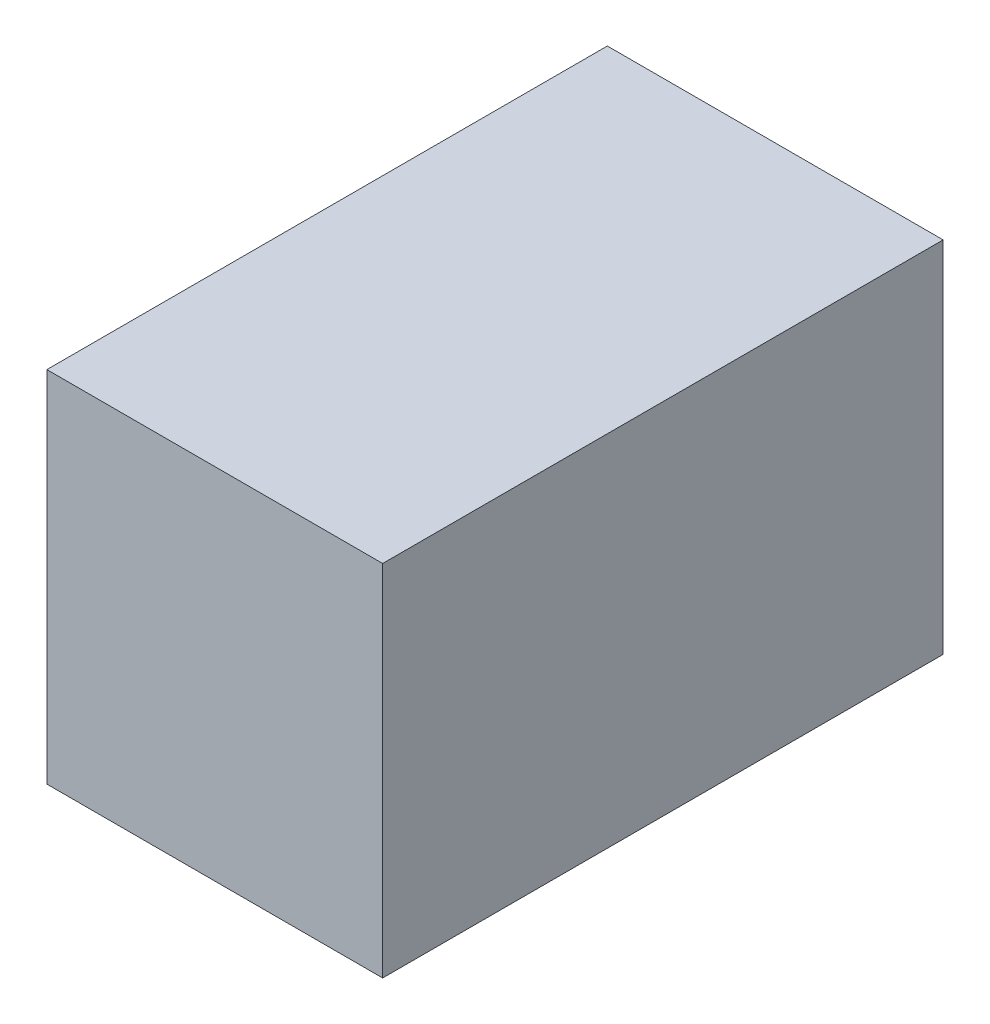
SolidWorks part; units mm, degrees
ref_plane "Front Plane" through (0, 0, 0) normal (0, 0, 1) x (1, 0, 0)
ref_plane "Top Plane" through (0, 0, 0) normal (0, 1, 0) x (1, 0, 0)
ref_plane "Right Plane" through (0, 0, 0) normal (1, 0, 0) x (0, 0, -1)
sketch "Sketch4" plane through (0, 0, 0) normal (1, 0, 0) x (0, 0, -1)
  line L1 (-15.525, 9.225) -> (15.525, 9.225)
  line L2 (-15.525, 9.225) -> (-15.525, -9.225)
  line L3 (-15.525, -9.225) -> (15.525, -9.225)
  line L4 (15.525, 9.225) -> (15.525, -9.225)
  line L5 (-15.525, 9.225) -> (15.525, -9.225) construction
  line L6 (-15.525, -9.225) -> (15.525, 9.225) construction
  point P0 (0, 0)
  dimension "D1" = 31.05
  dimension "D2" = 18.45
extrude "Boss-Extrude1" add sketch "Sketch4" along normal blind 19
shell "Shell1" thickness 2
sketch "Sketch5" plane through (0, 0, -17.525) normal (0, 0, -1) x (-1, 0, 0)
  line L0 (0, -11.225) -> (0, 11.225) construction
  line L1 (0, 9.225) -> (-12, 9.225)
  line L2 (-12, 9.225) -> (-12, -9.225)
  line L3 (-12, -9.225) -> (0, -9.225)
  line L4 (-21, 11.225) -> (0, 11.225) construction
  line L5 (-21, -11.225) -> (0, -11.225) construction
  line L6 (0, 9.225) -> (0, -9.225)
  dimension "D1" = 12
  dimension "D2" = 2
  dimension "D3" = 2
extrude "Cut-Extrude1" cut sketch "Sketch5" against normal up to surface (2 mm away) up to face at (9.5, 0, -15.525)
equation "\"terminalRad\"= 3mm"
equation "\"terminalLen\"= 10.5mm"
equation "\"threadlen\"=11"
